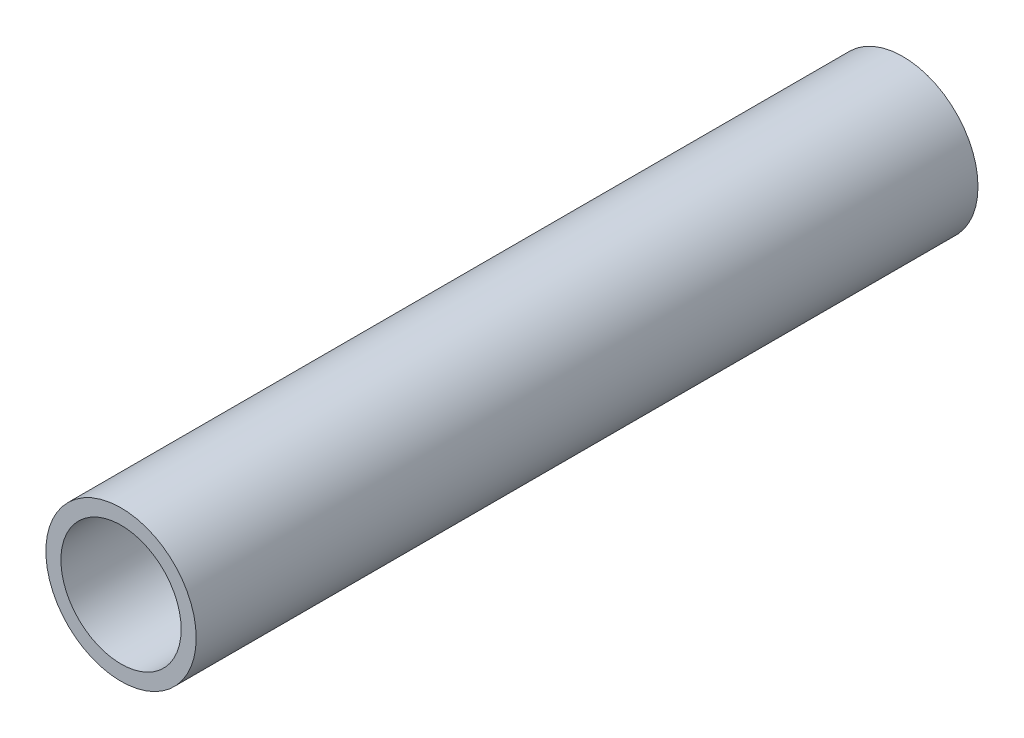
SolidWorks part; units mm, degrees
ref_plane "Alzado" through (0, 0, 0) normal (0, 0, 1) x (1, 0, 0)
ref_plane "Planta" through (0, 0, 0) normal (0, 1, 0) x (1, 0, 0)
ref_plane "Vista lateral" through (0, 0, 0) normal (1, 0, 0) x (0, 0, -1)
sketch "Croquis1" plane through (0, 0, 0) normal (0, 0, 1) x (1, 0, 0)
  circle A0 centre (0, 0) radius 10
  circle A1 centre (0, 0) radius 12.5
  dimension "D1" = 25
  dimension "D2" = 20
extrude "Saliente-Extruir1" add sketch "Croquis1" along normal blind 130
sketch "Croquis2" plane through (0, 0, 0) normal (1, 0, 0) x (0, 0, -1)
  line L0 (0, 0) -> (-7.5, 0) construction
  line L1 (0, -12.5) -> (0, 12.5) construction
  dimension "D1" = 7.5
